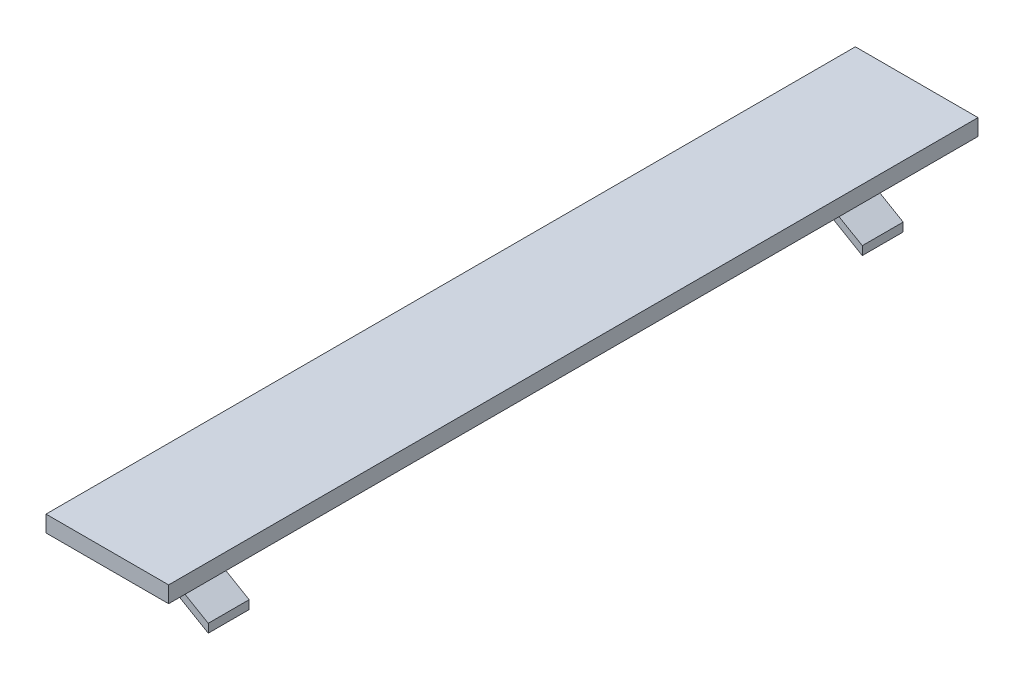
SolidWorks part; units mm, degrees
ref_plane "前视基准面" through (0, 0, 0) normal (0, 0, 1) x (1, 0, 0)
ref_plane "上视基准面" through (0, 0, 0) normal (0, 1, 0) x (1, 0, 0)
ref_plane "右视基准面" through (0, 0, 0) normal (1, 0, 0) x (0, 0, -1)
sketch "草图1" plane through (0, 0, 0) normal (0, 1, 0) x (1, 0, 0)
  line L1 (-10.2725, 9.1528) -> (4.7275, 9.1528)
  line L2 (-10.2725, 9.1528) -> (-10.2725, -89.8472)
  line L3 (-10.2725, -89.8472) -> (4.7275, -89.8472)
  line L4 (4.7275, 9.1528) -> (4.7275, -89.8472)
  dimension "D1" = 15
  dimension "D2" = 99
extrude "凸台-拉伸1" add sketch "草图1" along normal blind 2
sketch "草图3" plane through (0, 0, 0) normal (0, 0, 1) x (1, 0, 0)
  line L0 (-4.8105, 0) -> (4.7275, -5.5439)
  line L1 (-10.2725, 0) -> (4.7275, 0) construction
  line L2 (4.7275, -5.5439) -> (4.7275, -4.4911)
  line L3 (4.7275, -4.4911) -> (-2.9992, 0)
  line L4 (-2.9992, 0) -> (-4.8105, 0)
extrude "凸台-拉伸2" add sketch "草图3" along normal blind 5
ref_plane "基准面1" through (0, 0, 80) normal (0, 0, 1) x (1, 0, 0)
sketch "草图5" plane through (0, 0, 80) normal (0, 0, 1) x (1, 0, 0)
  line L0 (-4.8105, 0) -> (4.7275, -5.5439)
  line L2 (4.7275, -5.5439) -> (4.7275, -4.4911)
  line L3 (4.7275, -4.4911) -> (-2.9992, 0)
  line L4 (-2.9992, 0) -> (-4.8105, 0)
extrude "凸台-拉伸3" add sketch "草图5" along normal blind 5 contours L3 L4 L0 L2
